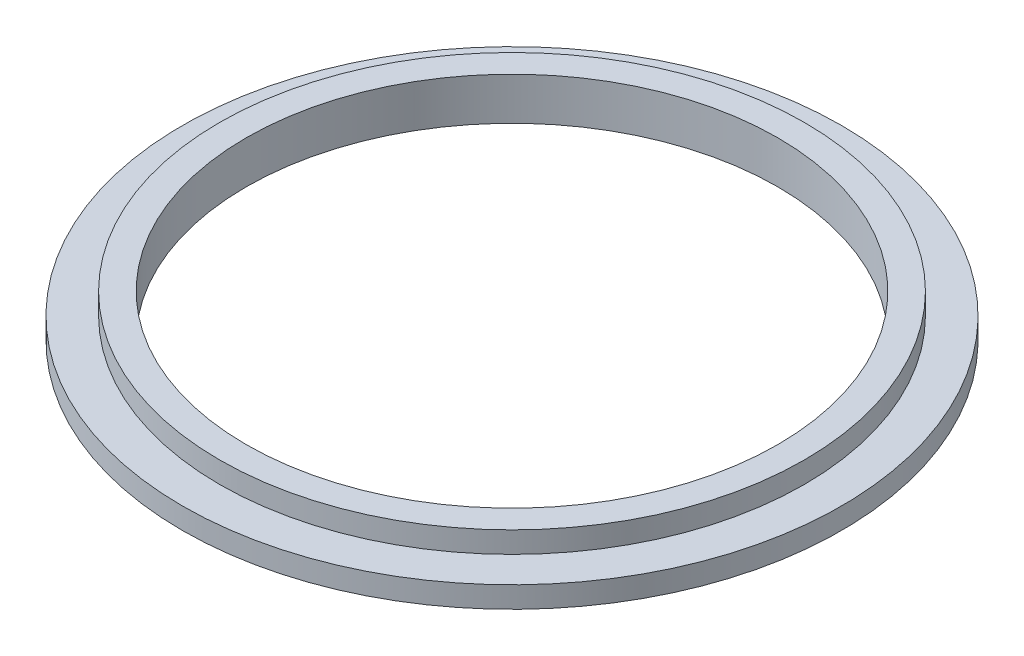
SolidWorks part; units mm, degrees
ref_plane "Front Plane" through (0, 0, 0) normal (0, 0, 1) x (1, 0, 0)
ref_plane "Top Plane" through (0, 0, 0) normal (0, 1, 0) x (1, 0, 0)
ref_plane "Right Plane" through (0, 0, 0) normal (1, 0, 0) x (0, 0, -1)
sketch "Sketch1" plane through (0, 0, 0) normal (0, 1, 0) x (1, 0, 0)
  circle A0 centre (0, 0) radius 250
  circle A1 centre (0, 0) radius 310
  dimension "D1" = 500
  dimension "D2" = 620
extrude "Boss-Extrude1" add sketch "Sketch1" along normal blind 20
sketch "Sketch2" plane through (0, 20, 0) normal (0, 1, 0) x (1, 0, 0)
  circle A0 centre (0, 0) radius 250
  circle A1 centre (0, 0) radius 275
  dimension "D1" = 550
  dimension "D2" = 500
extrude "Boss-Extrude2" add sketch "Sketch2" along normal blind 20
